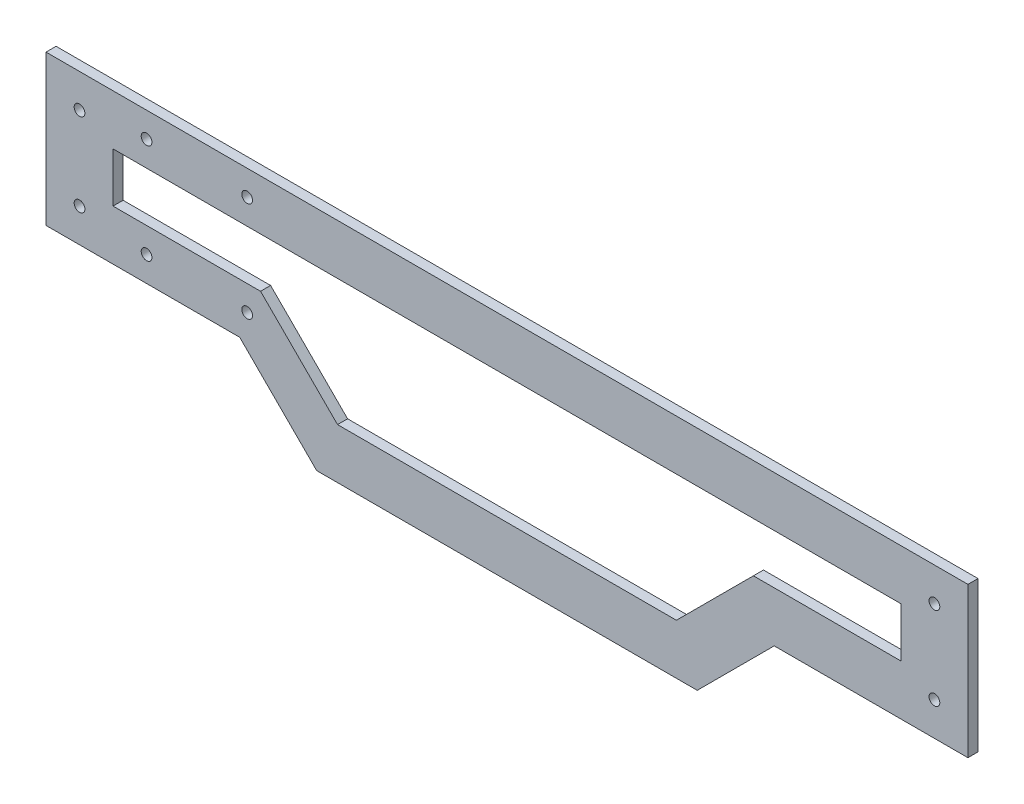
SolidWorks part; units mm, degrees
material "Thornel Mat VMA"
ref_plane "Front Plane" through (0, 0, 0) normal (0, 0, 1) x (1, 0, 0)
ref_plane "Top Plane" through (0, 0, 0) normal (0, 1, 0) x (1, 0, 0)
ref_plane "Right Plane" through (0, 0, 0) normal (1, 0, 0) x (0, 0, -1)
sketch "Sketch1" plane through (0, 0, 0) normal (0, 0, 1) x (1, 0, 0)
  line L0 (-21.5101, 432.2845) -> (253.4899, 432.2845)
  line L1 (-21.5101, 592.497) -> (-21.5101, 302.497) construction
  line L2 (253.4899, 302.497) -> (253.4899, 592.497) construction
  line L3 (253.4899, 432.2845) -> (253.4899, 387.497)
  line L4 (253.4899, 387.497) -> (195.7082, 387.497)
  line L5 (195.7082, 387.497) -> (172.7456, 364.5345)
  line L6 (172.7456, 364.5345) -> (59.2342, 364.5345)
  line L7 (59.2342, 364.5345) -> (36.2717, 387.497)
  line L8 (36.2717, 387.497) -> (-21.5101, 387.497)
  line L9 (-21.5101, 387.497) -> (-21.5101, 432.2845)
  line L10 (-21.5101, 442.2845) -> (-1.5101, 442.2845) construction
  line L11 (10.9163, 377.497) -> (-21.5101, 377.497) construction
  line L12 (32.1295, 377.497) -> (55.0921, 354.5345) construction
  line L13 (55.0921, 354.5345) -> (176.8877, 354.5345) construction
  line L14 (199.8503, 377.497) -> (176.8877, 354.5345) construction
  line L15 (253.4899, 377.497) -> (221.0635, 377.497) construction
  line L17 (-1.5101, 417.2845) -> (233.4899, 417.2845)
  line L18 (233.4899, 417.2845) -> (233.4899, 402.497)
  line L19 (233.4899, 402.497) -> (189.495, 402.497)
  line L20 (189.495, 402.497) -> (166.5324, 379.5345)
  line L21 (166.5324, 379.5345) -> (65.4475, 379.5345)
  line L22 (65.4475, 379.5345) -> (42.4849, 402.497)
  line L23 (42.4849, 402.497) -> (-1.5101, 402.497)
  line L24 (-1.5101, 402.497) -> (-1.5101, 417.2845)
  line L25 (233.4899, 302.497) -> (233.4899, 592.497) construction
  line L26 (-1.5101, 592.497) -> (-1.5101, 302.497) construction
  line L27 (-11.5101, 432.2845) -> (-11.5101, 387.497) construction
  line L28 (115.9899, 432.2845) -> (115.9899, 364.5345) construction
  circle A0 centre (-11.5101, 422.2845) radius 1.6
  circle A1 centre (-11.5101, 397.497) radius 1.6
  circle A2 centre (243.4899, 397.497) radius 1.6
  circle A3 centre (243.4899, 422.2845) radius 1.6
  point P44 (0, 0)
  dimension "D14" = 10
  dimension "D15" = 10
  dimension "D16" = 3.2
  dimension "D1" = 10
  dimension "D2" = 10
  dimension "D3" = 10
  dimension "D4" = 10
  dimension "D5" = 10
  dimension "D6" = 10
  dimension "D7" = 15
  dimension "D8" = 15
  dimension "D9" = 15
  dimension "D10" = 15
  dimension "D11" = 15
  dimension "D12" = 15
  dimension "D13" = 10
extrude "Extrude1" add sketch "Sketch1" along normal blind 3
sketch "Sketch2" plane through (0, 0, 0) normal (0, 0, -1) x (-1, 0, 0)
  line L0 (-253.4899, 432.2845) -> (21.5101, 432.2845) construction
  line L1 (-38.4899, 424.7845) -> (-8.4899, 424.7845) construction
  line L2 (-38.4899, 424.7845) -> (-38.4899, 394.997) construction
  line L3 (-38.4899, 394.997) -> (-8.4899, 394.997) construction
  line L4 (-8.4899, 424.7845) -> (-8.4899, 394.997) construction
  line L5 (21.5101, 387.497) -> (-36.2717, 387.497) construction
  line L6 (1.5101, 592.497) -> (1.5101, 302.497) construction
  line L7 (-48.4899, 390.8473) -> (-48.4899, 432.2845) construction
  circle A0 centre (-38.4899, 424.7845) radius 1.6
  circle A1 centre (-8.4899, 424.7845) radius 1.6
  circle A2 centre (-38.4899, 394.997) radius 1.6
  circle A3 centre (-8.4899, 394.997) radius 1.6
  dimension "D5" = 3.2
  dimension "D1" = 7.5
  dimension "D2" = 7.5
  dimension "D3" = 10
  dimension "D4" = 10
extrude "Cut-Extrude1" cut sketch "Sketch2" against normal blind 5
